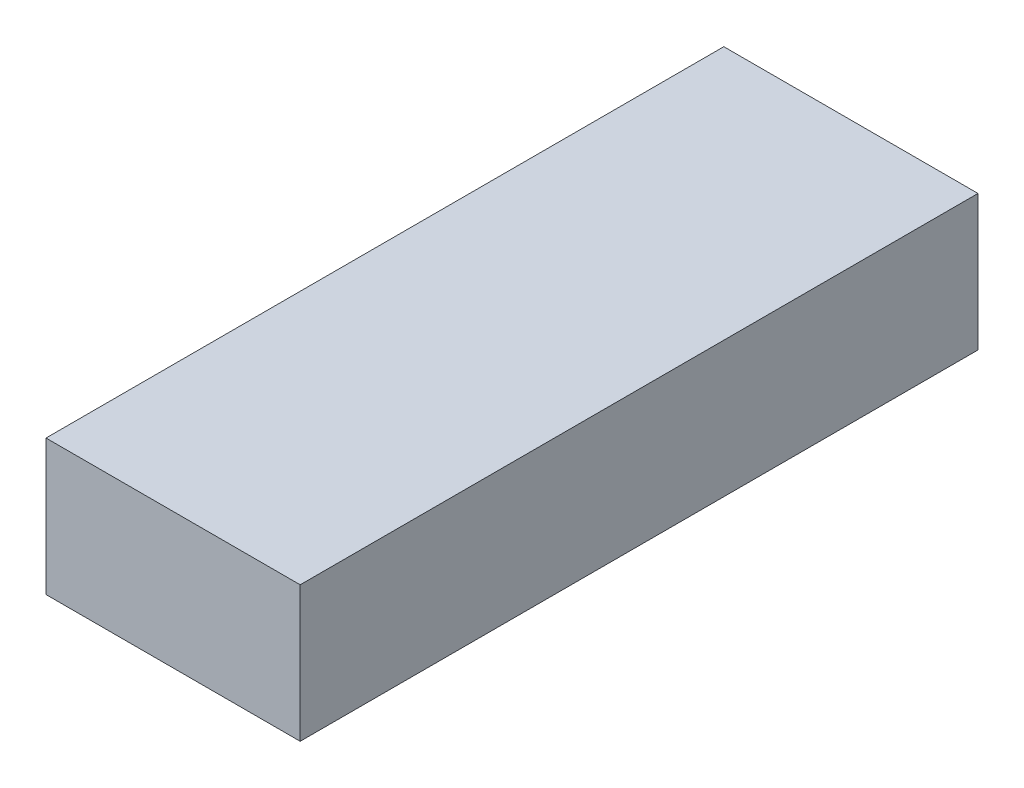
SolidWorks part; units mm, degrees
ref_plane "Alzado" through (0, 0, 0) normal (0, 0, 1) x (1, 0, 0)
ref_plane "Planta" through (0, 0, 0) normal (0, 1, 0) x (1, 0, 0)
ref_plane "Vista lateral" through (0, 0, 0) normal (1, 0, 0) x (0, 0, -1)
sketch "Croquis1" plane through (0, 0, 0) normal (0, 0, 1) x (1, 0, 0)
  line L1 (-75, -40) -> (75, -40)
  line L2 (-75, -40) -> (-75, 40)
  line L3 (-75, 40) -> (75, 40)
  line L4 (75, -40) -> (75, 40)
  line L5 (-75, -40) -> (75, 40) construction
  line L6 (-75, 40) -> (75, -40) construction
  line L7 (-70, -35) -> (70, -35)
  line L8 (-70, -35) -> (-70, 35)
  line L9 (-70, 35) -> (70, 35)
  line L10 (70, -35) -> (70, 35)
  line L11 (-70, -35) -> (70, 35) construction
  line L12 (-70, 35) -> (70, -35) construction
  point P0 (0, 0)
  point P6 (0, 0)
  dimension "D1" = 150
  dimension "D2" = 80
  dimension "D3" = 140
  dimension "D4" = 70
extrude "Saliente-Extruir1" add sketch "Croquis1" along normal blind 400
sketch "Croquis2" plane through (0, 0, 400) normal (0, 0, 1) x (1, 0, 0)
  line L0 (75, -40) -> (75, 40) construction
  line L1 (-75, -40) -> (75, -40) construction
  line L2 (-75, 40) -> (-75, -40) construction
  line L3 (75, 40) -> (-75, 40) construction
  line L4 (75, -40) -> (75, 40)
  line L5 (-75, -40) -> (75, -40)
  line L6 (-75, 40) -> (-75, -40)
  line L7 (75, 40) -> (-75, 40)
extrude "Saliente-Extruir2" add sketch "Croquis2" against normal blind 5
